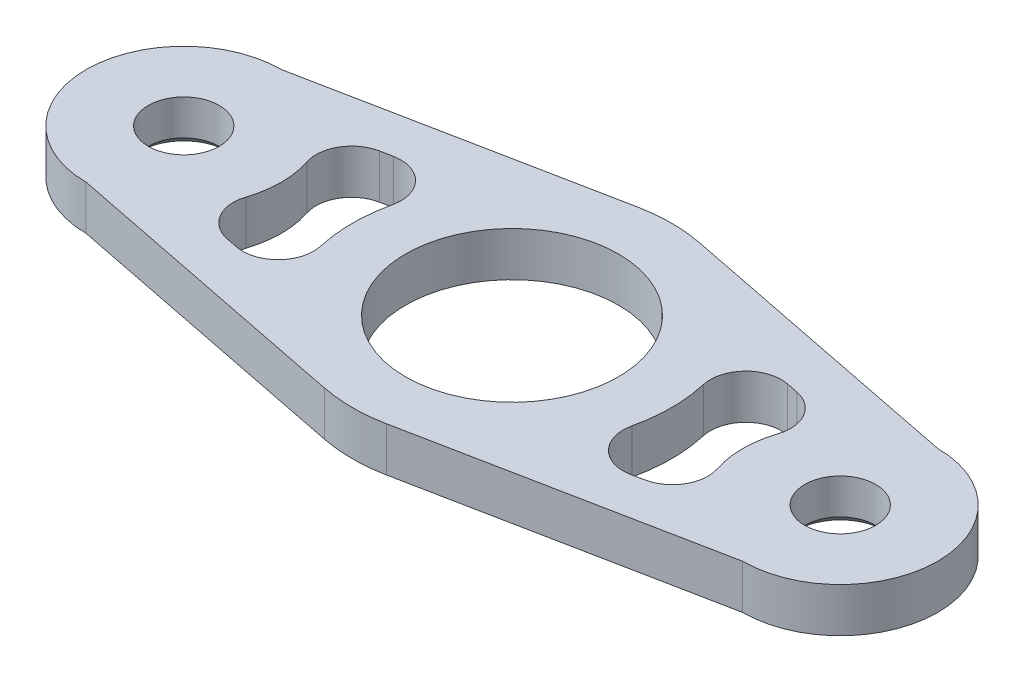
SolidWorks part; units mm, degrees
ref_plane "Front Plane" through (0, 0, 0) normal (0, 0, 1) x (1, 0, 0)
ref_plane "Top Plane" through (0, 0, 0) normal (0, 1, 0) x (1, 0, 0)
ref_plane "Right Plane" through (0, 0, 0) normal (1, 0, 0) x (0, 0, -1)
sketch "Sketch1" plane through (0, 0, 0) normal (0, 1, 0) x (1, 0, 0)
  line L0 (-37, 0) -> (0, 0) construction
  line L1 (0, 0) -> (0, 42.8424) construction
  line L2 (-37, 11) -> (-3.508, 17.6549)
  line L3 (-28.9542, 7.501) -> (-14.7447, 10.3244)
  line L4 (-28.9542, -7.501) -> (-14.7447, -10.3244)
  line L5 (-37, -11) -> (-3.508, -17.6549)
  line L6 (-36.0256, 6.0959) -> (-2.5336, 12.7507) construction
  line L7 (37, -11) -> (3.508, -17.6549)
  line L8 (28.9542, -7.501) -> (14.7447, -10.3244)
  line L9 (28.9542, 7.501) -> (14.7447, 10.3244)
  line L10 (37, 11) -> (3.508, 17.6549)
  circle A0 centre (0, 0) radius 12
  arc A1 (-14.7447, 10.3244) -> (-14.7447, -10.3244) centre (0, 0) ccw
  circle A2 centre (-37, 0) radius 4
  arc A3 (-37, 11) -> (-37, -11) centre (-37, 0) ccw
  arc A4 (-28.9542, -7.501) -> (-28.9542, 7.501) centre (-37, 0) ccw
  arc A5 (-3.508, -17.6549) -> (3.508, -17.6549) centre (0, 0) ccw
  arc A6 (28.9542, -7.501) -> (28.9542, 7.501) centre (37, 0) cw
  arc A7 (37, 11) -> (37, -11) centre (37, 0) cw
  circle A8 centre (37, 0) radius 4
  arc A9 (14.7447, 10.3244) -> (14.7447, -10.3244) centre (0, 0) cw
  arc A10 (3.508, 17.6549) -> (-3.508, 17.6549) centre (0, 0) ccw
  arc A11 (14.7447, -10.3244) -> (14.7447, 10.3244) centre (0, 0) ccw
  point P10 (-15.053, 17.2956)
  point P11 (-14.0963, 16.2404)
  dimension "D1" = 36
  dimension "D2" = 24
  dimension "D3" = 22
  dimension "D4" = 8
  dimension "D5" = 37
  dimension "D7" = 5
  dimension "D6" = 5
extrude "Boss-Extrude1" add sketch "Sketch1" along normal mid plane 5 contours L10 A10 L2 A3 L5 A5 L7 A7 A8 A2 A0 L4 A4 L3 A1 A9 L9 A6 L8
fillet "Fillet1" radius 4 8 edges at (14.7447, 0, 10.3244) (28.9542, 0, 7.501) (28.9542, 0, -7.501) (14.7447, 0, -10.3244) (-14.7447, 0, 10.3244) (-14.7447, 0, -10.3244) (-28.9542, 0, -7.501) (-28.9542, 0, 7.501)
chamfer "Chamfer1" distance 1 angle 45 2 edges at (37, -2.5, 4) (-37, -2.5, 4)
